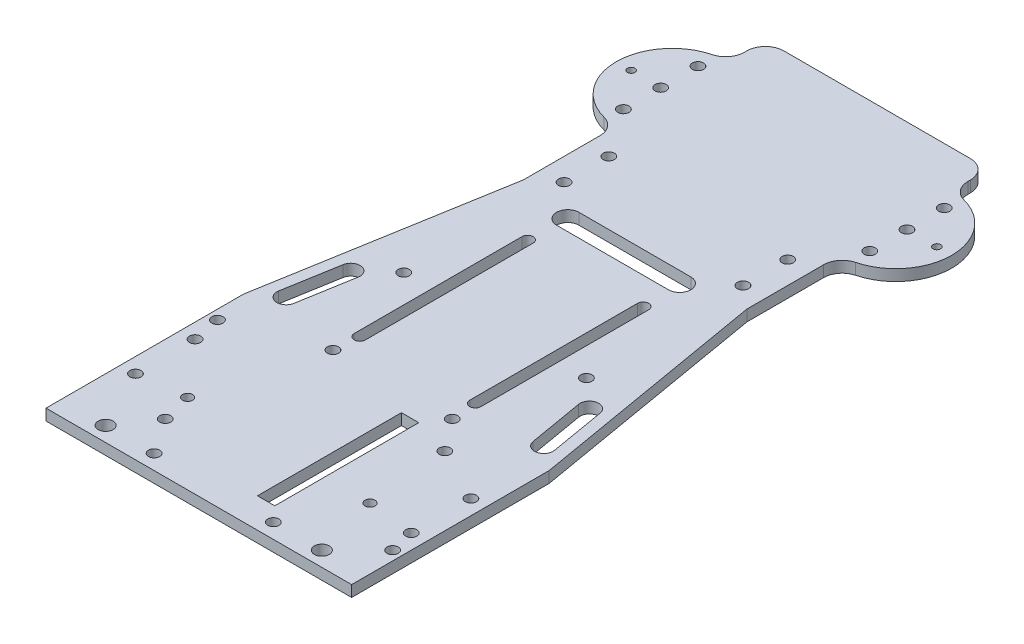
SolidWorks part; units mm, degrees
ref_plane "Front Plane" through (0, 0, 0) normal (0, 0, 1) x (1, 0, 0)
ref_plane "Top Plane" through (0, 0, 0) normal (0, 1, 0) x (1, 0, 0)
ref_plane "Right Plane" through (0, 0, 0) normal (1, 0, 0) x (0, 0, -1)
sketch "Sketch1" plane through (0, 0, 0) normal (0, 1, 0) x (1, 0, 0)
  line L0 (-41, 0) -> (41, 0)
  line L1 (41, 0) -> (41, 53)
  line L2 (41, 53) -> (30, 117.0625)
  line L3 (30, 117.0625) -> (30, 137.6351)
  line L4 (30, 176.3649) -> (30, 182)
  line L5 (-41, 0) -> (-41, 53)
  line L6 (-41, 53) -> (-30, 117.0625)
  line L7 (-30, 117.0625) -> (-30, 137.6351)
  line L8 (-30, 176.3649) -> (-30, 182)
  line L9 (-30, 182) -> (30, 182)
  arc A0 (33.75, 142.4763) -> (33.75, 171.5237) centre (30, 157) ccw
  arc A1 (-33.75, 171.5237) -> (-33.75, 142.4763) centre (-30, 157) ccw
  arc A2 (30, 137.6351) -> (33.75, 142.4763) centre (35, 137.6351) cw
  arc A3 (33.75, 171.5237) -> (30, 176.3649) centre (35, 176.3649) cw
  arc A4 (-30, 137.6351) -> (-33.75, 142.4763) centre (-35, 137.6351) ccw
  arc A5 (-30, 176.3649) -> (-33.75, 171.5237) centre (-35, 176.3649) cw
  point P20 (30, 172)
  point P25 (-30, 172)
  dimension "D10" = 15
  dimension "D11" = 15
  dimension "D14" = 60
  dimension "D16" = 5
  dimension "D17" = 5
  dimension "D18" = 5
  dimension "D19" = 5
  dimension "D1" = 82
  dimension "D2" = 53
  dimension "D3" = 53
  dimension "D4" = 182
  dimension "D5" = 41
  dimension "D6" = 60
  dimension "D7" = 30
  dimension "D8" = 65
  dimension "D9" = 65
  dimension "D12" = 10
  dimension "D13" = 10
  dimension "D15" = 30
extrude "Boss-Extrude1" add sketch "Sketch1" along normal blind 3
sketch "Sketch2" plane through (-30, 0, 0) normal (-1, 0, 0) x (0, 0, 1)
  line L0 (-182, 0) -> (-196, 13)
  line L1 (-196, 13) -> (-196, 16)
  line L2 (-196, 16) -> (-182, 3)
  line L3 (-182, 3) -> (-182, 0)
  dimension "D1" = 14
  dimension "D2" = 0
  dimension "D3" = 3
  dimension "D4" = 16
extrude "Boss-Extrude2" add sketch "Sketch2" against normal blind 60 separate body
ref_plane "Plane1" through (0, 16, 0) normal (0, 1, 0) x (1, 0, 0)
sketch "Sketch3" plane through (0, 16, 0) normal (0, 1, 0) x (1, 0, 0)
  line L0 (-30, 196) -> (30, 196)
  line L1 (30, 196) -> (34.8021, 210.9399)
  line L2 (25.2818, 224) -> (-25.2818, 224)
  line L3 (-34.8021, 210.9399) -> (-30, 196)
  arc A0 (-34.8021, 210.9399) -> (-25.2818, 224) centre (-25.2818, 214) cw
  arc A1 (34.8021, 210.9399) -> (25.2818, 224) centre (25.2818, 214) ccw
  point P8 (-39, 224)
  point P11 (39, 224)
  dimension "D2" = 10
  dimension "D3" = 10
  dimension "D1" = 78
  dimension "D4" = 28
extrude "Boss-Extrude3" add sketch "Sketch3" against normal blind 3
sketch "Sketch4" plane through (0, 3, 0) normal (0, 1, 0) x (1, 0, 0)
  line L0 (-41, 0) -> (41, 0) construction
  line L1 (-30, 137.6351) -> (-30, 117.0625) construction
  circle A0 centre (-24, 134) radius 1.5
  dimension "D1" = 3
  dimension "D2" = 134
  dimension "D3" = 6
extrude "Cut-Extrude1" cut sketch "Sketch4" against normal through all
pattern_linear "LPattern1" count 2 spacing 48 along (1, 0, 0) count 2 spacing 12 along (0, 0, 1) of "Cut-Extrude1"
sketch "Sketch6" plane through (0, 3, 0) normal (0, 1, 0) x (1, 0, 0)
  line L1 (-11.2663, 46.6284) -> (12.3853, 46.6284)
  line L2 (-11.2663, 46.6284) -> (-11.2663, -5.8269)
  line L3 (-11.2663, -5.8269) -> (12.3853, -5.8269)
  line L4 (12.3853, 46.6284) -> (12.3853, -5.8269)
extrude "Cut-Extrude2" cut sketch "Sketch6" against normal through all
sketch "Sketch8" plane through (-11.2663, 0, 0) normal (1, 0, 0) x (0, 0, -1)
  line L1 (46.6284, 0) -> (0, 0)
  line L2 (46.6284, 0) -> (46.6284, 3)
  line L3 (46.6284, 3) -> (0, 3)
  line L4 (0, 0) -> (0, 3)
extrude "Boss-Extrude4" add sketch "Sketch8" along normal blind 19
sketch "Sketch9" plane through (7.7337, 0, 0) normal (1, 0, 0) x (0, 0, -1)
  line L0 (46.6284, 3) -> (0, 3) construction
  line L1 (0, 0) -> (8, 0)
  line L2 (0, 0) -> (0, 3)
  line L3 (0, 3) -> (8, 3)
  line L4 (8, 0) -> (8, 3)
extrude "Boss-Extrude5" add sketch "Sketch9" along normal up to next (4.6516 mm away)
sketch "Sketch12" plane through (0, 0, 0) normal (0, -1, 0) x (1, 0, 0)
  circle A0 centre (-16, -4) radius 1.5
  circle A1 centre (16, -4) radius 1.5
extrude "Cut-Extrude4" cut sketch "Sketch12" against normal through all
sketch "Sketch13" plane through (0, 3, 0) normal (0, 1, 0) x (1, 0, 0)
  circle A0 centre (41, 157) radius 1
  circle A1 centre (-41, 157) radius 1
  arc A2 (-33.75, 171.5237) -> (-33.75, 142.4763) centre (-30, 157) ccw construction
  circle A4 centre (33, 157) radius 1.5
  circle A5 centre (-33, 156.9132) radius 1.5
  circle A6 centre (33, 147) radius 1.5
  circle A7 centre (33, 167) radius 1.5
  circle A8 centre (-33, 166.9132) radius 1.5
  circle A9 centre (-33, 146.9132) radius 1.5
  dimension "D1" = 2
  dimension "D2" = 2
  dimension "D3" = 82
  dimension "D4" = 11
  dimension "D5" = 3
  dimension "D6" = 3
  dimension "D7" = 8
  dimension "D8" = 8
  dimension "D9" = 3
  dimension "D10" = 3
  dimension "D11" = 3
  dimension "D12" = 3
  dimension "D13" = 10
  dimension "D14" = 10
  dimension "D15" = 10
  dimension "D16" = 10
extrude "Cut-Extrude5" cut sketch "Sketch13" against normal through all
sketch "Sketch14" plane through (0, 0, 0) normal (0, -1, 0) x (1, 0, 0)
  circle A0 centre (-24.5, -21.5) radius 1.35
  circle A3 centre (24.54, -21.4) radius 1.35
  dimension "D1" = 2.7
  dimension "D2" = 2.7
extrude "Cut-Extrude6" cut sketch "Sketch14" against normal through all
sketch "Sketch15" plane through (0, 0, 0) normal (0, -1, 0) x (1, 0, 0)
  line L0 (41, 0) -> (41, -53) construction
  line L1 (-41, 0) -> (41, 0) construction
  circle A0 centre (22.5, -43.5) radius 1.5
  circle A1 centre (38.5, -13.5) radius 1.5
  dimension "D1" = 3
  dimension "D2" = 2.5
  dimension "D3" = 13.5
  dimension "D4" = 3
  dimension "D5" = 18.5
  dimension "D6" = 43.5
extrude "Cut-Extrude7" cut sketch "Sketch15" against normal through all
sketch "Sketch16" plane through (0, 0, 0) normal (0, -1, 0) x (1, 0, 0)
  line L0 (-41, 0) -> (41, 0) construction
  line L1 (-41, -53) -> (-41, 0) construction
  circle A0 centre (-22.5, -13.5) radius 1.5
  circle A1 centre (-38.5, -43.5) radius 1.5
  dimension "D1" = 3
  dimension "D2" = 3
  dimension "D3" = 13.5
  dimension "D4" = 18.5
  dimension "D5" = 2.5
  dimension "D6" = 43.5
extrude "Cut-Extrude8" cut sketch "Sketch16" against normal through all
sketch "Sketch17" plane through (0, 0, 0) normal (0, -1, 0) x (1, 0, 0)
  line L0 (34.561, -58) -> (32.0225, -72.7836) construction
  line L1 (37.0249, -58.4231) -> (34.4865, -73.2067)
  line L2 (32.097, -57.5769) -> (29.5586, -72.3606)
  line L3 (0, -56.6862) -> (0, -32.0518) construction
  line L4 (41, 0) -> (41, -53) construction
  line L5 (41, -53) -> (30, -117.0625) construction
  line L6 (-34.561, -58) -> (-32.0225, -72.7836) construction
  line L7 (-37.0249, -58.4231) -> (-34.4865, -73.2067)
  line L8 (-41, 0) -> (41, 0) construction
  line L9 (-32.097, -57.5769) -> (-29.5586, -72.3606)
  arc A0 (37.0249, -58.4231) -> (32.097, -57.5769) centre (34.561, -58) ccw
  arc A1 (29.5586, -72.3606) -> (34.4865, -73.2067) centre (32.0225, -72.7836) ccw
  arc A2 (-37.0249, -58.4231) -> (-32.097, -57.5769) centre (-34.561, -58) cw
  arc A3 (-29.5586, -72.3606) -> (-34.4865, -73.2067) centre (-32.0225, -72.7836) cw
  point P2 (33.2917, -65.3918)
  point P17 (-33.2917, -65.3918)
  dimension "D2" = 2.5
  dimension "D4" = 58
  dimension "D1" = 3
  dimension "D3" = 15
  dimension "D5" = 41
extrude "Cut-Extrude9" cut sketch "Sketch17" against normal through all
sketch "Sketch19" plane through (0, 0, 0) normal (0, -1, 0) x (-1, 0, 0)
  circle A0 centre (24.5, 79.5) radius 1.5
  circle A1 centre (-24.5, 79.5) radius 1.5
  dimension "D1" = 3
  dimension "D2" = 3
extrude "Cut-Extrude10" cut sketch "Sketch19" against normal through all
sketch "Sketch20" plane through (30, 0, 0) normal (1, 0, 0) x (0, 0, -1)
  line L1 (182, 0) -> (224, 0)
  line L2 (182, 0) -> (182, 16)
  line L3 (182, 16) -> (224, 16)
  line L4 (224, 0) -> (224, 16)
extrude "Cut-Extrude11" cut sketch "Sketch20" against normal up to next and the other way up to next
fillet "Fillet1" radius 5 1 edges at (30, 1.5, -182)
fillet "Fillet2" radius 5 1 edges at (-30, 1.5, -182)
sketch "Sketch21" plane through (0, 3, 0) normal (0, 1, 0) x (1, 0, 0)
  line L0 (41, 0) -> (41, 53) construction
  line L1 (-41, 53) -> (-41, 0) construction
  circle A0 centre (37, 20) radius 1.5
  circle A1 centre (16, 20) radius 2.4 construction
  circle A2 centre (-37, 20) radius 1.5
  circle A3 centre (-37, 36) radius 1.5
  circle A4 centre (37, 36) radius 1.5
  dimension "D1" = 4
  dimension "D2" = 3
  dimension "D3" = 0
  dimension "D6" = 4
  dimension "D7" = 16
  dimension "D8" = 74
  dimension "D9" = 4
  dimension "D4" = 2
  dimension "D5" = 2
extrude "Cut-Extrude12" cut sketch "Sketch21" against normal through all
sketch "Sketch22" plane through (0, 3, 0) normal (0, 1, 0) x (1, 0, 0)
  line L0 (15.5, 58.7) -> (15.5, 103.7) construction
  line L1 (14, 58.7) -> (14, 103.7)
  line L2 (17, 58.7) -> (17, 103.7)
  line L3 (-15.5, 58.7) -> (-15.5, 103.7) construction
  line L4 (-17, 58.7) -> (-17, 103.7)
  line L5 (-14, 58.7) -> (-14, 103.7)
  line L6 (-20.5, 63.7) -> (-8.5, 63.7) construction
  line L7 (20.5, 63.7) -> (8.5, 63.7) construction
  arc A0 (14, 58.7) -> (17, 58.7) centre (15.5, 58.7) ccw
  arc A1 (17, 103.7) -> (14, 103.7) centre (15.5, 103.7) ccw
  arc A2 (-17, 58.7) -> (-14, 58.7) centre (-15.5, 58.7) ccw
  arc A3 (-14, 103.7) -> (-17, 103.7) centre (-15.5, 103.7) ccw
  circle A4 centre (-15.5, 98.2) radius 2 construction
  circle A5 centre (15.5, 98.2) radius 2 construction
  point P2 (15.5, 81.2)
  point P7 (-15.5, 81.2)
  dimension "D1" = 1.5
  dimension "D4" = 5
  dimension "D5" = 1.5
  dimension "D7" = 5
  dimension "D2" = 0
  dimension "D3" = 45
  dimension "D6" = 0
  dimension "D8" = 45
extrude "Cut-Extrude13" cut sketch "Sketch22" against normal through all
sketch "Sketch23" plane through (0, 3, 0) normal (0, 1, 0) x (1, 0, 0)
  circle A0 centre (-16, 52) radius 1.5
  circle A1 centre (16, 52) radius 1.5
  dimension "D1" = 3
  dimension "D2" = 3
extrude "Cut-Extrude14" cut sketch "Sketch23" against normal through all
sketch "Sketch24" plane through (0, 3, 0) normal (0, 1, 0) x (1, 0, 0)
  line L0 (15, 114) -> (-15, 114) construction
  line L1 (15, 111) -> (-15, 111)
  line L2 (15, 117) -> (-15, 117)
  line L6 (25, 182) -> (-25, 182) construction
  line L8 (-30, 137.6351) -> (-30, 117.0625) construction
  line L9 (30, 117.0625) -> (30, 137.6351) construction
  arc A0 (15, 111) -> (15, 117) centre (15, 114) ccw
  arc A1 (-15, 117) -> (-15, 111) centre (-15, 114) ccw
  point P2 (0, 114)
  point P9 (-30, 122.9481)
  dimension "D2" = 15
  dimension "D4" = 3
  dimension "D1" = 15
  dimension "D3" = 65
extrude "Cut-Extrude15" cut sketch "Sketch24" against normal through all
sketch "Sketch25" plane through (0, 3, 0) normal (0, 1, 0) x (1, 0, 0)
  circle A0 centre (-29, 4) radius 2
  circle A1 centre (29, 4) radius 2
  dimension "D1" = 4
  dimension "D2" = 4
extrude "Cut-Extrude16" cut sketch "Sketch25" against normal through all
